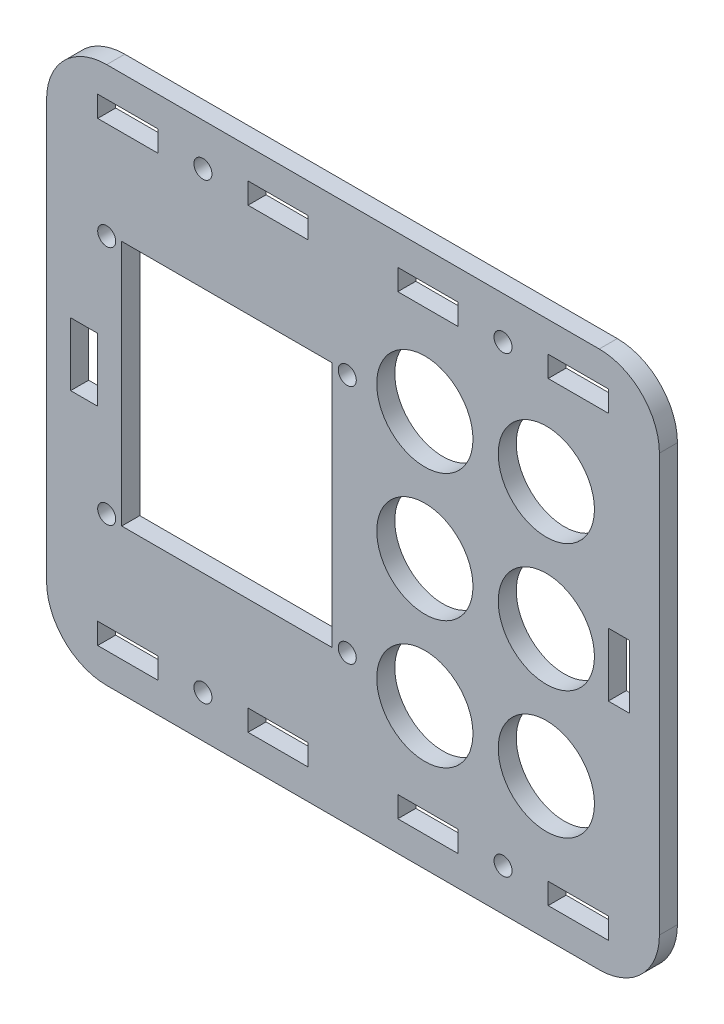
SolidWorks part; units mm, degrees
ref_plane "Front Plane" through (0, 0, 0) normal (0, 0, 1) x (1, 0, 0)
ref_plane "Top Plane" through (0, 0, 0) normal (0, 1, 0) x (1, 0, 0)
ref_plane "Right Plane" through (0, 0, 0) normal (1, 0, 0) x (0, 0, -1)
sketch "Model" plane through (0, 0, 0) normal (0, 0, 1) x (1, 0, 0)
  line L0 (79.9, -77.4) -> (79.9, -80.9)
  line L1 (79.9, -80.9) -> (89.9, -80.9)
  line L2 (89.9, -80.9) -> (89.9, -77.4)
  line L3 (89.9, -77.4) -> (79.9, -77.4)
  line L4 (30, -77.4) -> (30, -80.9)
  line L5 (30, -80.9) -> (40, -80.9)
  line L6 (40, -80.9) -> (40, -77.4)
  line L7 (40, -77.4) -> (30, -77.4)
  line L8 (79.9, -1.5) -> (79.9, -5)
  line L9 (79.9, -5) -> (89.9, -5)
  line L10 (89.9, -5) -> (89.9, -1.5)
  line L11 (89.9, -1.5) -> (79.9, -1.5)
  line L12 (30, -1.5) -> (30, -5)
  line L13 (30, -5) -> (40, -5)
  line L14 (40, -5) -> (40, -1.5)
  line L15 (40, -1.5) -> (30, -1.5)
  line L16 (89.9, -35.95) -> (89.9, -46.45)
  line L17 (89.9, -46.45) -> (93.4, -46.45)
  line L18 (93.4, -46.45) -> (93.4, -35.95)
  line L19 (93.4, -35.95) -> (89.9, -35.95)
  line L20 (6.5, 3.5) -> (88.4, 3.5)
  line L21 (98.4, -6.5) -> (98.4, -75.9)
  line L22 (6.5, -85.9) -> (88.4, -85.9)
  line L23 (-3.5, -6.5) -> (-3.5, -75.9)
  line L24 (0.5, -46.45) -> (5, -46.45)
  line L25 (5, -46.45) -> (5, -35.95)
  line L26 (5, -35.95) -> (0.5, -35.95)
  line L27 (0.5, -35.95) -> (0.5, -46.45)
  line L28 (5, -5) -> (15, -5)
  line L29 (15, -5) -> (15, -1.5)
  line L30 (15, -1.5) -> (5, -1.5)
  line L31 (5, -1.5) -> (5, -5)
  line L32 (54.9, -5) -> (64.9, -5)
  line L33 (64.9, -5) -> (64.9, -1.5)
  line L34 (64.9, -1.5) -> (54.9, -1.5)
  line L35 (54.9, -1.5) -> (54.9, -5)
  line L36 (5, -80.9) -> (15, -80.9)
  line L37 (15, -80.9) -> (15, -77.4)
  line L38 (15, -77.4) -> (5, -77.4)
  line L39 (5, -77.4) -> (5, -80.9)
  line L40 (54.9, -77.4) -> (54.9, -80.9)
  line L41 (54.9, -80.9) -> (64.9, -80.9)
  line L42 (64.9, -80.9) -> (64.9, -77.4)
  line L43 (64.9, -77.4) -> (54.9, -77.4)
  line L44 (9, -61.7) -> (44, -61.7)
  line L45 (44, -61.7) -> (44, -20.7)
  line L46 (44, -20.7) -> (9, -20.7)
  line L47 (9, -20.7) -> (9, -61.7)
  circle A0 centre (79.6, -20) radius 8
  circle A1 centre (79.6, -62.4) radius 8
  circle A2 centre (79.6, -41.2) radius 8
  circle A4 centre (46.5, -61.2) radius 1.5
  circle A5 centre (6.5, -21.2) radius 1.5
  circle A6 centre (72.4, -78.9) radius 1.5
  circle A7 centre (22.5, -3.5) radius 1.5
  circle A8 centre (72.4, -3.5) radius 1.5
  circle A9 centre (22.5, -78.9) radius 1.5
  circle A10 centre (6.5, -61.2) radius 1.5
  circle A11 centre (46.5, -21.2) radius 1.5
  circle A12 centre (59.4, -41.2) radius 8
  circle A13 centre (59.4, -62.4) radius 8
  circle A14 centre (59.4, -20) radius 8
  arc A15 (-3.5, -75.9) -> (6.5, -85.9) centre (6.5, -75.9) ccw
  arc A16 (88.4, -85.9) -> (98.4, -75.9) centre (88.4, -75.9) ccw
  arc A17 (98.4, -6.5) -> (88.4, 3.5) centre (88.4, -6.5) ccw
  arc A18 (6.5, 3.5) -> (-3.5, -6.5) centre (6.5, -6.5) ccw
  dimension "D7" = 5
  dimension "D10" = 10
  dimension "D14" = 2.5
  dimension "D15" = 2.5
  dimension "D20" = 39
  dimension "D22" = 39
  dimension "D24" = 18.8
  dimension "D25" = 18.8
  dimension "D26" = 3.5
  dimension "D29" = 7.5
  dimension "D33" = 4
  dimension "D1" = 84.9
  dimension "D2" = 72.4
  dimension "D3" = 15.7
  dimension "D4" = 15.7
  dimension "D5" = 7.5
  dimension "D6" = 14.9
  dimension "D8" = 5
  dimension "D9" = 5
  dimension "D11" = 4
  dimension "D12" = 1.5
  dimension "D13" = 1.5
  dimension "D16" = 14.75
  dimension "D17" = 14.75
  dimension "D18" = 14.75
  dimension "D19" = 14.75
  dimension "D21" = 39
  dimension "D23" = 18.8
  dimension "D27" = 39.9
  dimension "D28" = 32.4
  dimension "D30" = 10
  dimension "D31" = 14.9
  dimension "D32" = 7.5
  dimension "D34" = 4.5
extrude "Boss-Extrude1" add sketch "Model" along normal blind 3 contours L20 A18 L23 A15 L22 A16 L21 A17 L3 L2 L1 L0 L7 L6 L5 L4 L11 L10 L9 L8 L15 L14 L13 L12 L19 L18 L17 L16 L27 L26 L25 L24 L31 L30 L29 L28 L35 L34 L33 L32 L39 L38 | A0 | L46 L47 L44 L45
